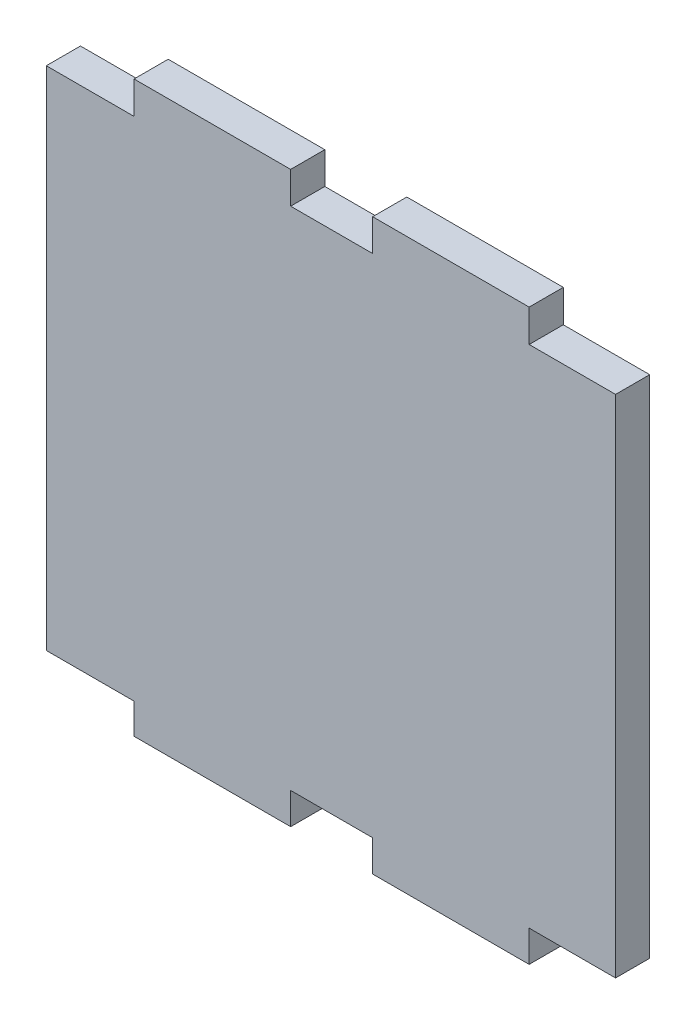
SolidWorks part; units mm, degrees
ref_plane "Front Plane" through (0, 0, 0) normal (0, 0, 1) x (1, 0, 0)
ref_plane "Top Plane" through (0, 0, 0) normal (0, 1, 0) x (1, 0, 0)
ref_plane "Right Plane" through (0, 0, 0) normal (1, 0, 0) x (0, 0, -1)
sketch "Sketch2" plane through (0, 0, 0) normal (0, 0, 1) x (1, 0, 0)
  line L1 (0, 0) -> (200, 0)
  line L2 (0, 0) -> (0, 200)
  line L3 (0, 200) -> (200, 200)
  line L4 (200, 0) -> (200, 200)
extrude "Boss-Extrude1" add sketch "Sketch2" along normal blind 12
sketch "Sketch3" plane through (0, 0, 0) normal (0, 0, -1) x (-1, 0, 0)
  line L0 (-200, 188.6116) -> (-169.64, 188.6116)
  line L1 (-200, 0) -> (-200, 200) construction
  line L2 (-169.64, 188.6116) -> (-169.64, 200)
  line L3 (-200, 200) -> (0, 200) construction
  line L5 (-30.8313, 200) -> (-30.8313, 188.6116)
  line L6 (-30.8313, 188.6116) -> (0, 188.6116)
  line L7 (0, 200) -> (0, 0) construction
  line L8 (-200, 0) -> (-200, 11.0438)
  line L9 (-200, 11.0438) -> (-169.64, 11.0438)
  line L10 (-114.6594, 200) -> (-85.8508, 200)
  line L11 (-114.6594, 200) -> (-114.6594, 188.7981)
  line L12 (-114.6594, 188.7981) -> (-85.8508, 188.7981)
  line L13 (-85.8508, 188.7981) -> (-85.8508, 200)
  line L14 (-169.64, 11.0438) -> (-169.64, 0)
  line L15 (0, 0) -> (-200, 0) construction
  line L16 (0, 0) -> (0, 10.6992)
  line L17 (0, 10.6992) -> (-30.8313, 10.6992)
  line L18 (-30.8313, 10.6992) -> (-30.8313, 0)
  line L19 (-114.6594, 0) -> (-114.6594, 11.0438)
  line L20 (-114.6594, 0) -> (-85.8508, 0)
  line L21 (-85.8508, 0) -> (-85.8508, 11.0438)
  line L22 (-85.8508, 11.0438) -> (-114.6594, 11.0438)
  line L23 (-169.64, 200) -> (-200, 200)
  line L24 (-200, 200) -> (-200, 188.6116)
  line L26 (-30.8313, 200) -> (0, 200)
  line L27 (-30.8313, 0) -> (0, 0)
  line L28 (0, 200) -> (0, 188.6116)
  line L29 (-200, 0) -> (-169.64, 0)
extrude "Cut-Extrude4" cut sketch "Sketch3" against normal through all contours L24 L0 L2 L23 | L10 L13 L12 L11 | L28 L6 L5 L26 | L27 L16 L17 L18 | L19 L22 L21 L20 | L29 L14 L9 L8
